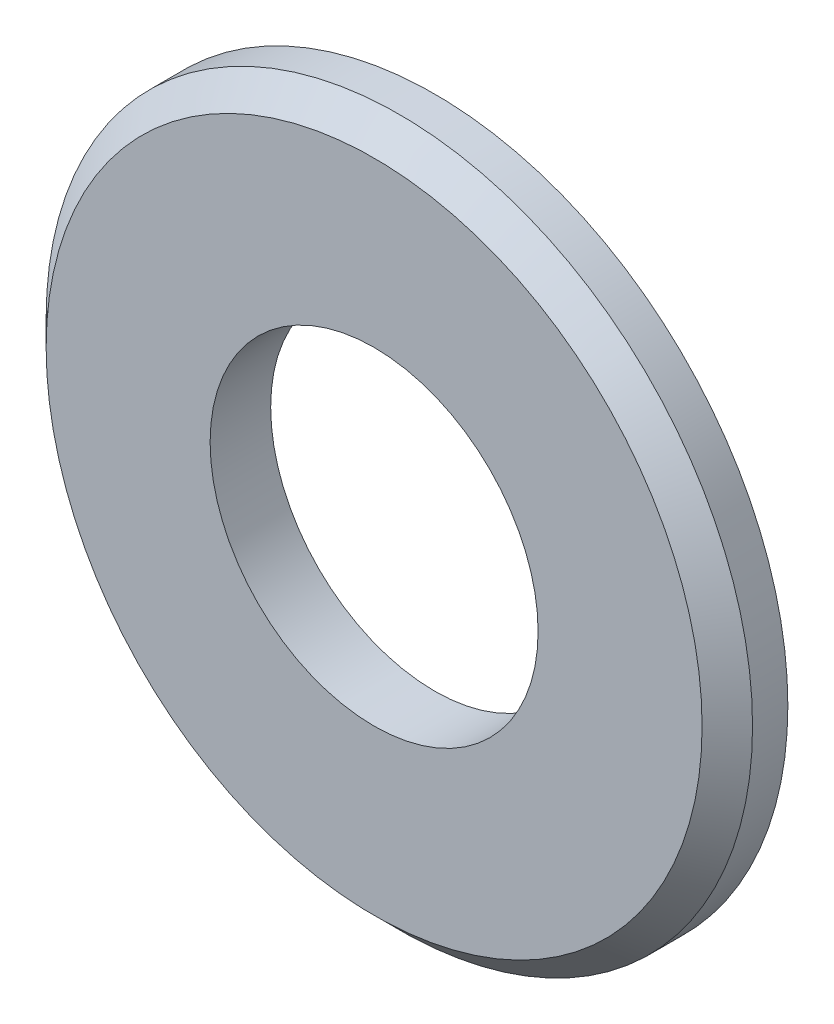
SolidWorks part; units mm, degrees
ref_plane "Plan1" through (0, 0, 0) normal (0, 0, 1) x (1, 0, 0)
ref_plane "Plan2" through (0, 0, 0) normal (0, 1, 0) x (1, 0, 0)
ref_plane "Plan3" through (0, 0, 0) normal (1, 0, 0) x (0, 0, -1)
sketch "Esquisse1" plane through (0, 0, 0) normal (0, 0, 1) x (1, 0, 0)
  circle A0 centre (0, 0) radius 3.25
  circle A1 centre (0, 0) radius 7
  dimension "D1" = 6.5
  dimension "D2" = 14
extrude "Base-Extrusion" add sketch "Esquisse1" along normal blind 1.2
chamfer "Chanfrein1" distance 0.5 angle 45
